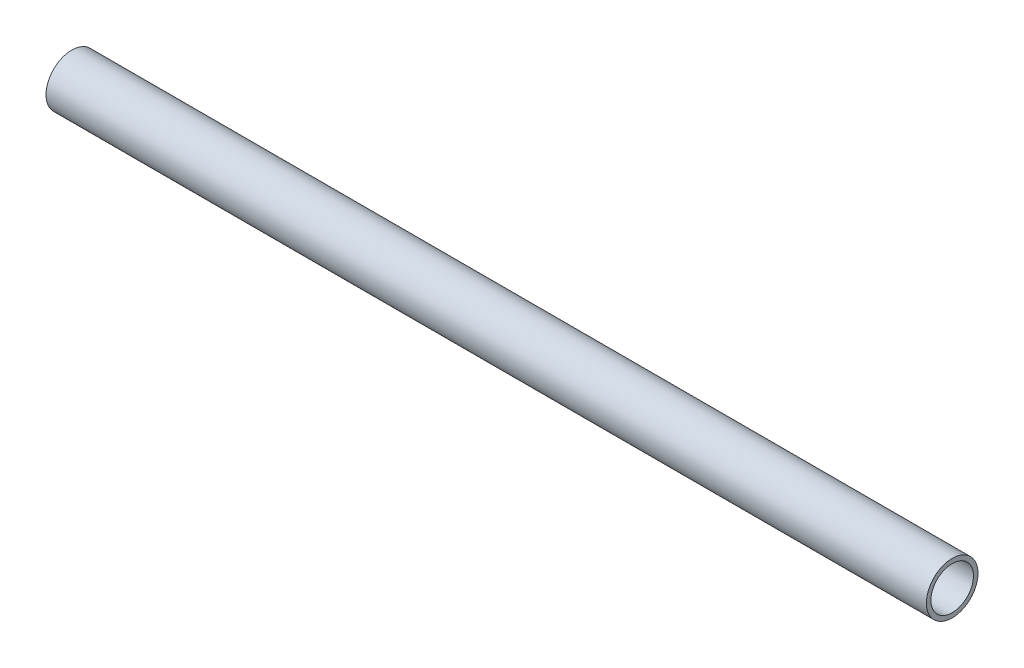
SolidWorks part; units mm, degrees
ref_plane "Front Plane" through (0, 0, 0) normal (0, 0, 1) x (1, 0, 0)
ref_plane "Top Plane" through (0, 0, 0) normal (0, 1, 0) x (1, 0, 0)
ref_plane "Right Plane" through (0, 0, 0) normal (1, 0, 0) x (0, 0, -1)
sketch "Sketch2" plane through (0, 0, 0) normal (0, 0, 1) x (1, 0, 0)
  line L1 (-148.4881, 657.2504) -> (-256.7466, 657.2504)
other "Pipe 0.5 SCH 40(1)"
ref_plane "Plane1" through (-148.4881, 657.2504, 0) normal (-1, 0, 0) x (0, -1, 0)
sketch "Sketch1" plane through (-148.4881, 657.2504, 0) normal (-1, 0, 0) x (0, -1, 0)
  circle A0 centre (0, 0) radius 2.6162
  circle A1 centre (0, 0) radius 3.175
  point P5 (0, 0)
  dimension "In_dia" = 5.2324
  dimension "Out_dia" = 6.35
